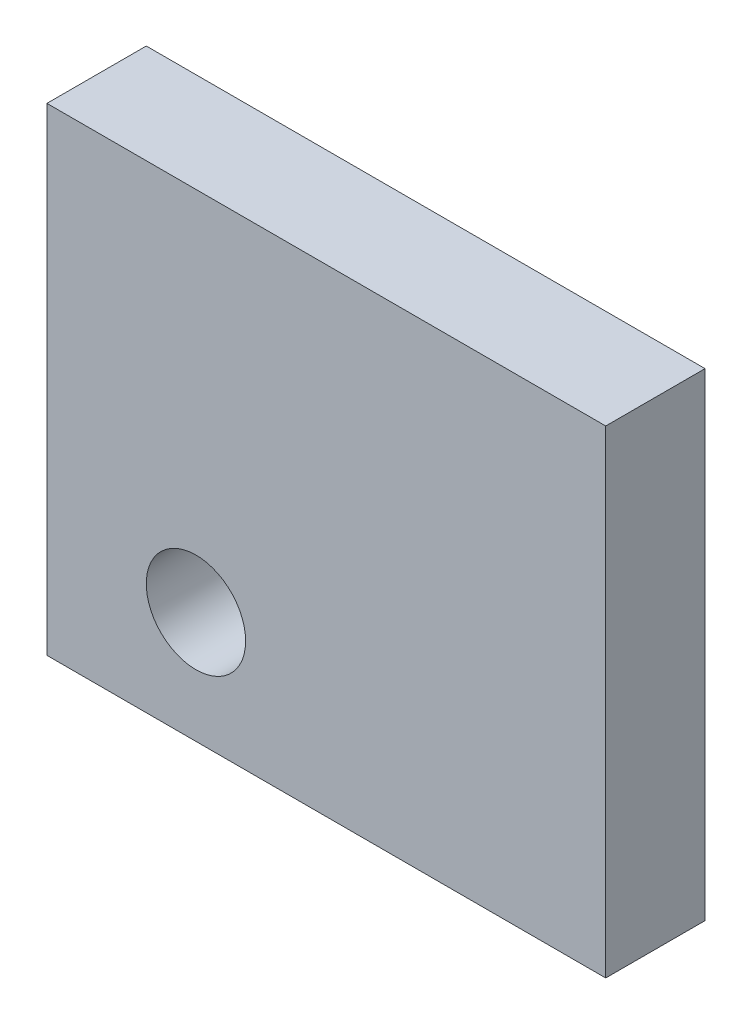
SolidWorks part; units mm, degrees
ref_plane "Front Plane" through (0, 0, 0) normal (0, 0, 1) x (1, 0, 0)
ref_plane "Top Plane" through (0, 0, 0) normal (0, 1, 0) x (1, 0, 0)
ref_plane "Right Plane" through (0, 0, 0) normal (1, 0, 0) x (0, 0, -1)
sketch "Sketch1" plane through (0, 0, 0) normal (0, 0, 1) x (1, 0, 0)
  line L1 (-22.5, -13.5) -> (22.5, -13.5)
  line L2 (-22.5, -13.5) -> (-22.5, 25)
  line L3 (-22.5, 25) -> (22.5, 25)
  line L4 (22.5, -13.5) -> (22.5, 25)
  line L5 (0, 25) -> (0, -13.5) construction
  line L6 (-22.5, 0) -> (22.5, 0) construction
  point P0 (0, 0)
  dimension "D1" = 25
  dimension "D2" = 45
  dimension "D3" = 13.5
extrude "Boss-Extrude1" add sketch "Sketch1" along normal blind 8
sketch "Sketch2" plane through (0, 0, 8) normal (0, 0, 1) x (1, 0, 0)
  line L0 (22.5, 0) -> (-10.5, 0) construction
  line L2 (22.5, 25) -> (-22.5, 25) construction
  line L3 (22.5, -4.5) -> (-10.5, -4.5) construction
  circle A0 centre (-10.5, -4.5) radius 4
  dimension "D2" = 8
  dimension "D1" = 29.5
  dimension "D3" = 33
extrude "Cut-Extrude1" cut sketch "Sketch2" against normal up to surface (8 mm away) up to face at (0, 5.75, 0)
